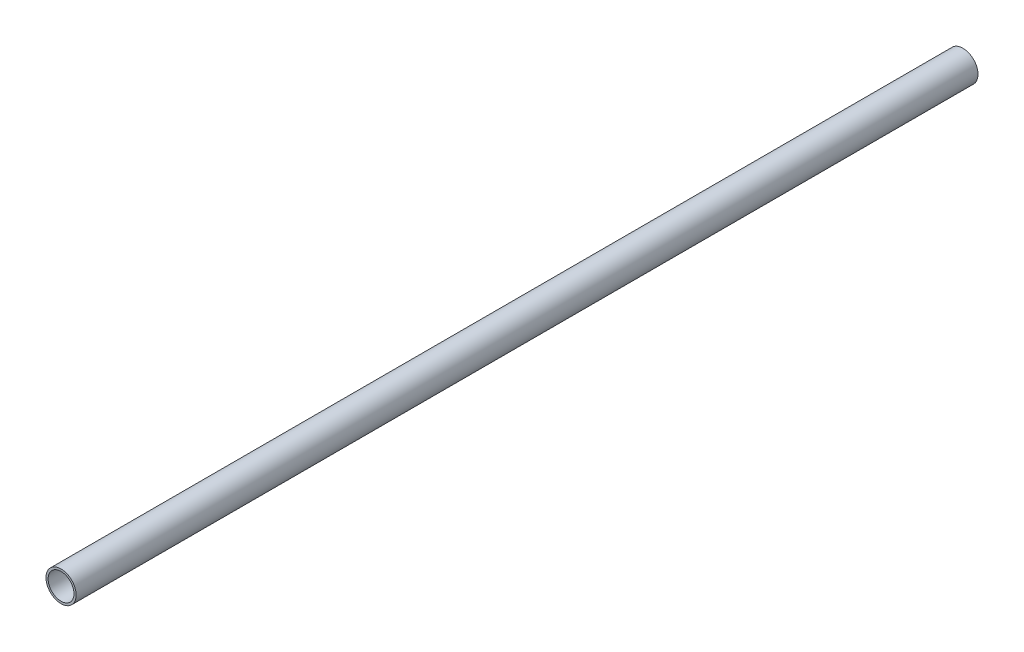
SolidWorks part; units mm, degrees
material "Thornel VCB-20 Carbon Cloth"
ref_plane "Front Plane" through (0, 0, 0) normal (0, 0, 1) x (1, 0, 0)
ref_plane "Top Plane" through (0, 0, 0) normal (0, 1, 0) x (1, 0, 0)
ref_plane "Right Plane" through (0, 0, 0) normal (1, 0, 0) x (0, 0, -1)
sketch "Sketch1" plane through (0, 0, 0) normal (0, 0, 1) x (1, 0, 0)
  circle A0 centre (0, 0) radius 9.525
  circle A1 centre (0, 0) radius 11.1125
  dimension "D1" = 19.05
  dimension "D2" = 22.225
extrude "Boss-Extrude1" add sketch "Sketch1" along normal mid plane 664.718
